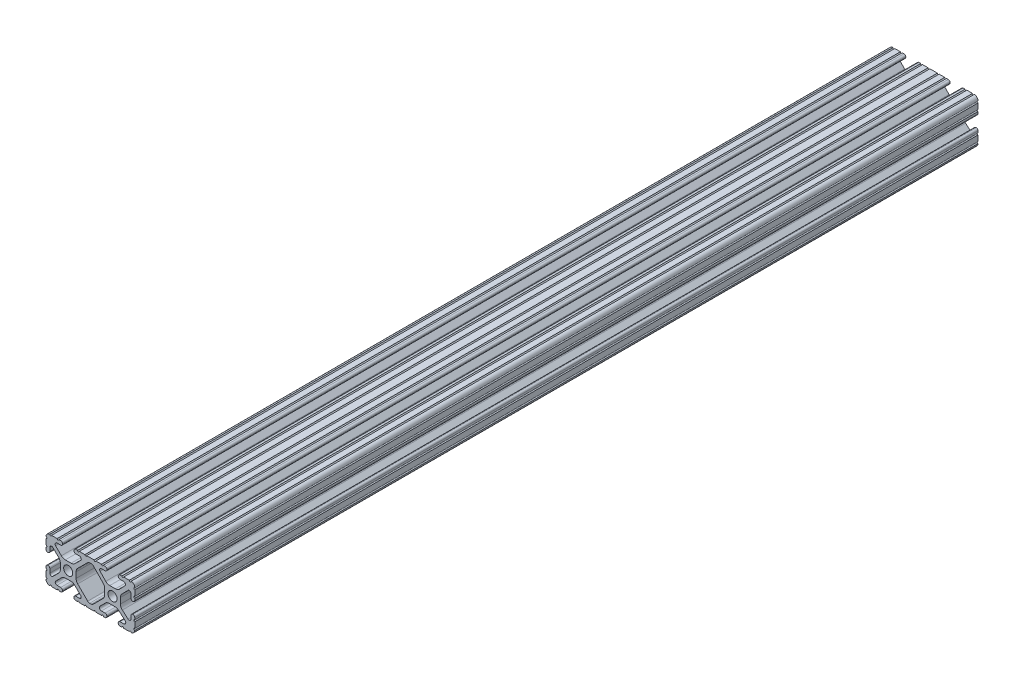
SolidWorks part; units mm, degrees
ref_plane "Front Plane" through (0, 0, 0) normal (0, 0, 1) x (1, 0, 0)
ref_plane "Top Plane" through (0, 0, 0) normal (0, 1, 0) x (1, 0, 0)
ref_plane "Right Plane" through (0, 0, 0) normal (1, 0, 0) x (0, 0, -1)
sketch "Sketch1" plane through (0, 0, 0) normal (0, 0, 1) x (1, 0, 0)
  line L0 (-7.2595, -3.8694) -> (-1.5457, -9.5728)
  line L1 (-8.1915, 1.6223) -> (-8.1915, -1.6223)
  line L2 (-1.504, 9.5765) -> (-7.252, 3.8768)
  line L3 (0.5515, 10.033) -> (-0.3952, 10.033)
  line L4 (7.2829, 3.8459) -> (1.6756, 9.5611)
  line L5 (8.1915, -1.6223) -> (8.1915, 1.6223)
  line L6 (1.5457, -9.5728) -> (7.2595, -3.8694)
  line L7 (-0.4332, -10.033) -> (0.4332, -10.033)
  line L8 (18.0171, 12.7) -> (16.9875, 12.7)
  line L9 (15.9385, 11.651) -> (15.9385, 11.5392)
  line L10 (16.9875, 10.4902) -> (19.1164, 10.4902)
  line L11 (19.8441, 8.7652) -> (16.619, 5.4551)
  line L12 (14.3449, 4.4958) -> (11.0833, 4.4958)
  line L13 (8.817, 5.4472) -> (5.5642, 8.7627)
  line L14 (6.2894, 10.4902) -> (8.4125, 10.4902)
  line L15 (9.4615, 11.5392) -> (9.4615, 11.651)
  line L16 (8.4125, 12.7) -> (7.3829, 12.7)
  line L17 (6.3669, 12.7) -> (3.1496, 12.7)
  line L18 (2.1336, 12.7) -> (-2.1336, 12.7)
  line L19 (-3.1496, 12.7) -> (-6.3669, 12.7)
  line L20 (-7.3829, 12.7) -> (-8.4125, 12.7)
  line L21 (-9.4615, 11.651) -> (-9.4615, 11.5392)
  line L22 (-8.4125, 10.4902) -> (-6.2836, 10.4902)
  line L23 (-5.5326, 8.6661) -> (-8.81, 5.4163)
  line L24 (-11.0455, 4.4958) -> (-14.3545, 4.4958)
  line L25 (-16.59, 5.4163) -> (-19.8674, 8.6661)
  line L26 (-19.1164, 10.4902) -> (-16.9875, 10.4902)
  line L27 (-15.9385, 11.5392) -> (-15.9385, 11.651)
  line L28 (-16.9875, 12.7) -> (-18.0171, 12.7)
  line L29 (-19.0331, 12.7) -> (-22.2504, 12.7)
  line L30 (-25.4, 9.5504) -> (-25.4, 6.3331)
  line L31 (-25.4, 5.3171) -> (-25.4, 4.2375)
  line L32 (-24.401, 3.2385) -> (-24.2392, 3.2385)
  line L33 (-23.1902, 4.2875) -> (-23.1902, 6.3347)
  line L34 (-21.434, 7.0665) -> (-18.148, 3.8082)
  line L35 (-17.2085, 1.5536) -> (-17.2085, -1.6952)
  line L36 (-18.1405, -3.9423) -> (-21.4316, -7.2274)
  line L37 (-23.1902, -6.498) -> (-23.1902, -4.2875)
  line L38 (-24.2392, -3.2385) -> (-24.351, -3.2385)
  line L39 (-25.4, -4.2875) -> (-25.4, -5.3171)
  line L40 (-25.4, -6.3331) -> (-25.4, -9.5504)
  line L41 (-22.2504, -12.7) -> (-19.0331, -12.7)
  line L42 (-18.0171, -12.7) -> (-16.9875, -12.7)
  line L43 (-15.9384, -11.651) -> (-15.9384, -11.5392)
  line L44 (-16.9875, -10.4902) -> (-19.1164, -10.4902)
  line L45 (-19.8341, -8.7551) -> (-16.4966, -5.4237)
  line L46 (-14.2536, -4.4958) -> (-11.1464, -4.4958)
  line L47 (-8.9034, -5.4237) -> (-5.5659, -8.7551)
  line L48 (-6.2836, -10.4902) -> (-8.4125, -10.4902)
  line L49 (-9.4616, -11.5392) -> (-9.4616, -11.651)
  line L50 (-8.4125, -12.7) -> (-7.3829, -12.7)
  line L51 (-6.3669, -12.7) -> (-3.1496, -12.7)
  line L52 (-2.1336, -12.7) -> (2.1336, -12.7)
  line L53 (3.1496, -12.7) -> (6.3669, -12.7)
  line L54 (7.3829, -12.7) -> (8.4125, -12.7)
  line L55 (9.4616, -11.651) -> (9.4616, -11.5392)
  line L56 (8.4125, -10.4902) -> (6.2894, -10.4902)
  line L57 (5.4807, -8.5353) -> (8.5979, -5.4237)
  line L58 (10.8409, -4.4958) -> (14.1026, -4.4958)
  line L59 (16.1879, -5.2766) -> (19.8682, -8.4822)
  line L60 (19.1164, -10.4902) -> (16.9875, -10.4902)
  line L61 (15.9384, -11.5392) -> (15.9384, -11.651)
  line L62 (16.9875, -12.7) -> (18.0171, -12.7)
  line L63 (19.0331, -12.7) -> (22.2504, -12.7)
  line L64 (25.4, -9.5504) -> (25.4, -6.3331)
  line L65 (25.4, -5.3171) -> (25.4, -4.2375)
  line L66 (24.401, -3.2385) -> (24.1892, -3.2385)
  line L67 (23.1902, -4.2375) -> (23.1902, -6.1559)
  line L68 (21.584, -6.8869) -> (18.2982, -4.025)
  line L69 (17.2085, -1.6308) -> (17.2085, 1.6308)
  line L70 (18.1094, 3.8465) -> (21.5263, 7.3534)
  line L71 (23.1902, 6.6769) -> (23.1902, 4.2375)
  line L72 (24.1892, 3.2385) -> (24.401, 3.2385)
  line L73 (25.4, 4.2375) -> (25.4, 5.3171)
  line L74 (25.4, 6.3332) -> (25.4, 9.5504)
  line L75 (22.2504, 12.7) -> (19.0331, 12.7)
  circle A0 centre (-12.7, 0) radius 2.6035
  circle A1 centre (12.7, 0) radius 2.6035
  arc A2 (-1.5457, -9.5728) -> (-0.4332, -10.033) centre (-0.4332, -8.4582) ccw
  arc A3 (-8.1915, -1.6223) -> (-7.2595, -3.8694) centre (-5.0165, -1.6223) ccw
  arc A4 (-7.252, 3.8768) -> (-8.1915, 1.6223) centre (-5.0165, 1.6223) ccw
  arc A5 (-0.3952, 10.033) -> (-1.504, 9.5765) centre (-0.3952, 8.4582) ccw
  arc A6 (1.6756, 9.5611) -> (0.5515, 10.033) centre (0.5515, 8.4582) ccw
  arc A7 (8.1915, 1.6223) -> (7.2829, 3.8459) centre (5.0165, 1.6223) ccw
  arc A8 (7.2595, -3.8694) -> (8.1915, -1.6223) centre (5.0165, -1.6223) ccw
  arc A9 (0.4332, -10.033) -> (1.5457, -9.5728) centre (0.4332, -8.4582) ccw
  arc A10 (18.0171, 12.7) -> (19.0331, 12.7) centre (18.5251, 12.7) ccw
  arc A11 (16.9875, 12.7) -> (15.9385, 11.651) centre (16.9875, 11.651) ccw
  arc A12 (15.9385, 11.5392) -> (16.9875, 10.4902) centre (16.9875, 11.5392) ccw
  arc A13 (19.8441, 8.7652) -> (19.1164, 10.4902) centre (19.1164, 9.4742) ccw
  arc A14 (14.3449, 4.4958) -> (16.619, 5.4551) centre (14.3449, 7.6708) ccw
  arc A15 (8.817, 5.4472) -> (11.0833, 4.4958) centre (11.0833, 7.6708) ccw
  arc A16 (6.2894, 10.4902) -> (5.5642, 8.7627) centre (6.2894, 9.4742) ccw
  arc A17 (8.4125, 10.4902) -> (9.4615, 11.5392) centre (8.4125, 11.5392) ccw
  arc A18 (9.4615, 11.651) -> (8.4125, 12.7) centre (8.4125, 11.651) ccw
  arc A19 (6.3669, 12.7) -> (7.3829, 12.7) centre (6.8749, 12.7) ccw
  arc A20 (2.1336, 12.7) -> (3.1496, 12.7) centre (2.6416, 12.7) ccw
  arc A21 (-3.1496, 12.7) -> (-2.1336, 12.7) centre (-2.6416, 12.7) ccw
  arc A22 (-7.3829, 12.7) -> (-6.3669, 12.7) centre (-6.8749, 12.7) ccw
  arc A23 (-8.4125, 12.7) -> (-9.4615, 11.651) centre (-8.4125, 11.651) ccw
  arc A24 (-9.4615, 11.5392) -> (-8.4125, 10.4902) centre (-8.4125, 11.5392) ccw
  arc A25 (-5.5326, 8.6661) -> (-6.2836, 10.4902) centre (-6.2836, 9.4235) ccw
  arc A26 (-11.0455, 4.4958) -> (-8.81, 5.4163) centre (-11.0455, 7.6708) ccw
  arc A27 (-16.59, 5.4163) -> (-14.3545, 4.4958) centre (-14.3545, 7.6708) ccw
  arc A28 (-19.1164, 10.4902) -> (-19.8674, 8.6661) centre (-19.1164, 9.4235) ccw
  arc A29 (-16.9875, 10.4902) -> (-15.9385, 11.5392) centre (-16.9875, 11.5392) ccw
  arc A30 (-15.9385, 11.651) -> (-16.9875, 12.7) centre (-16.9875, 11.651) ccw
  arc A31 (-19.0331, 12.7) -> (-18.0171, 12.7) centre (-18.5251, 12.7) ccw
  arc A32 (-23.2664, 12.6998) -> (-22.2504, 12.7) centre (-22.7584, 12.7) ccw
  arc A33 (-23.2664, 12.6998) -> (-25.3998, 10.5664) centre (-23.2918, 10.5918) ccw
  arc A34 (-25.4, 9.5504) -> (-25.3998, 10.5664) centre (-25.4, 10.0584) ccw
  arc A35 (-25.4, 5.3171) -> (-25.4, 6.3331) centre (-25.4, 5.8251) ccw
  arc A36 (-25.4, 4.2375) -> (-24.401, 3.2385) centre (-24.401, 4.2375) ccw
  arc A37 (-24.2392, 3.2385) -> (-23.1902, 4.2875) centre (-24.2392, 4.2875) ccw
  arc A38 (-21.434, 7.0665) -> (-23.1902, 6.3347) centre (-22.1596, 6.3347) ccw
  arc A39 (-17.2085, 1.5536) -> (-18.148, 3.8082) centre (-20.3835, 1.5536) ccw
  arc A40 (-18.1405, -3.9423) -> (-17.2085, -1.6952) centre (-20.3835, -1.6952) ccw
  arc A41 (-23.1902, -6.498) -> (-21.4316, -7.2274) centre (-22.1596, -6.498) ccw
  arc A42 (-23.1902, -4.2875) -> (-24.2392, -3.2385) centre (-24.2392, -4.2875) ccw
  arc A43 (-24.351, -3.2385) -> (-25.4, -4.2875) centre (-24.351, -4.2875) ccw
  arc A44 (-25.4, -6.3331) -> (-25.4, -5.3171) centre (-25.4, -5.8251) ccw
  arc A45 (-25.3998, -10.5664) -> (-25.4, -9.5504) centre (-25.4, -10.0584) ccw
  arc A46 (-25.3998, -10.5664) -> (-23.2664, -12.6998) centre (-23.2918, -10.5918) ccw
  arc A47 (-22.2504, -12.7) -> (-23.2664, -12.6998) centre (-22.7584, -12.7) ccw
  arc A48 (-18.0171, -12.7) -> (-19.0331, -12.7) centre (-18.5251, -12.7) ccw
  arc A49 (-16.9875, -12.7) -> (-15.9384, -11.651) centre (-16.9875, -11.651) ccw
  arc A50 (-15.9384, -11.5392) -> (-16.9875, -10.4902) centre (-16.9875, -11.5392) ccw
  arc A51 (-19.8341, -8.7551) -> (-19.1164, -10.4902) centre (-19.1164, -9.4742) ccw
  arc A52 (-14.2536, -4.4958) -> (-16.4966, -5.4237) centre (-14.2536, -7.6708) ccw
  arc A53 (-8.9034, -5.4237) -> (-11.1464, -4.4958) centre (-11.1464, -7.6708) ccw
  arc A54 (-6.2836, -10.4902) -> (-5.5659, -8.7551) centre (-6.2836, -9.4742) ccw
  arc A55 (-8.4125, -10.4902) -> (-9.4616, -11.5392) centre (-8.4125, -11.5392) ccw
  arc A56 (-9.4616, -11.651) -> (-8.4125, -12.7) centre (-8.4125, -11.651) ccw
  arc A57 (-6.3669, -12.7) -> (-7.3829, -12.7) centre (-6.8749, -12.7) ccw
  arc A58 (-2.1336, -12.7) -> (-3.1496, -12.7) centre (-2.6416, -12.7) ccw
  arc A59 (3.1496, -12.7) -> (2.1336, -12.7) centre (2.6416, -12.7) ccw
  arc A60 (7.3829, -12.7) -> (6.3669, -12.7) centre (6.8749, -12.7) ccw
  arc A61 (8.4125, -12.7) -> (9.4616, -11.651) centre (8.4125, -11.651) ccw
  arc A62 (9.4616, -11.5392) -> (8.4125, -10.4902) centre (8.4125, -11.5392) ccw
  arc A63 (5.4807, -8.5353) -> (6.2894, -10.4902) centre (6.2894, -9.3455) ccw
  arc A64 (10.8409, -4.4958) -> (8.5979, -5.4237) centre (10.8409, -7.6708) ccw
  arc A65 (16.1879, -5.2766) -> (14.1026, -4.4958) centre (14.1026, -7.6708) ccw
  arc A66 (19.1164, -10.4902) -> (19.8682, -8.4822) centre (19.1164, -9.3455) ccw
  arc A67 (16.9875, -10.4902) -> (15.9384, -11.5392) centre (16.9875, -11.5392) ccw
  arc A68 (15.9384, -11.651) -> (16.9875, -12.7) centre (16.9875, -11.651) ccw
  arc A69 (19.0331, -12.7) -> (18.0171, -12.7) centre (18.5251, -12.7) ccw
  arc A70 (23.2664, -12.6998) -> (22.2504, -12.7) centre (22.7584, -12.7) ccw
  arc A71 (23.2664, -12.6998) -> (25.3998, -10.5664) centre (23.2918, -10.5918) ccw
  arc A72 (25.4, -9.5504) -> (25.3998, -10.5664) centre (25.4, -10.0584) ccw
  arc A73 (25.4, -5.3171) -> (25.4, -6.3331) centre (25.4, -5.8251) ccw
  arc A74 (25.4, -4.2375) -> (24.401, -3.2385) centre (24.401, -4.2375) ccw
  arc A75 (24.1892, -3.2385) -> (23.1902, -4.2375) centre (24.1892, -4.2375) ccw
  arc A76 (21.584, -6.8869) -> (23.1902, -6.1559) centre (22.2207, -6.1559) ccw
  arc A77 (17.2085, -1.6308) -> (18.2982, -4.025) centre (20.3835, -1.6308) ccw
  arc A78 (18.1094, 3.8465) -> (17.2085, 1.6308) centre (20.3835, 1.6308) ccw
  arc A79 (23.1902, 6.6769) -> (21.5263, 7.3534) centre (22.2207, 6.6769) ccw
  arc A80 (23.1902, 4.2375) -> (24.1892, 3.2385) centre (24.1892, 4.2375) ccw
  arc A81 (24.401, 3.2385) -> (25.4, 4.2375) centre (24.401, 4.2375) ccw
  arc A82 (25.4, 6.3332) -> (25.4, 5.3171) centre (25.4, 5.8251) ccw
  arc A83 (25.3998, 10.5664) -> (25.4, 9.5504) centre (25.4, 10.0584) ccw
  arc A84 (25.3998, 10.5664) -> (23.2664, 12.6998) centre (23.2918, 10.5918) ccw
  arc A85 (22.2504, 12.7) -> (23.2664, 12.6998) centre (22.7584, 12.7) ccw
  point P248 (0, 10.033)
extrude "Boss-Extrude1" add sketch "Sketch1" along normal mid plane 482.6
